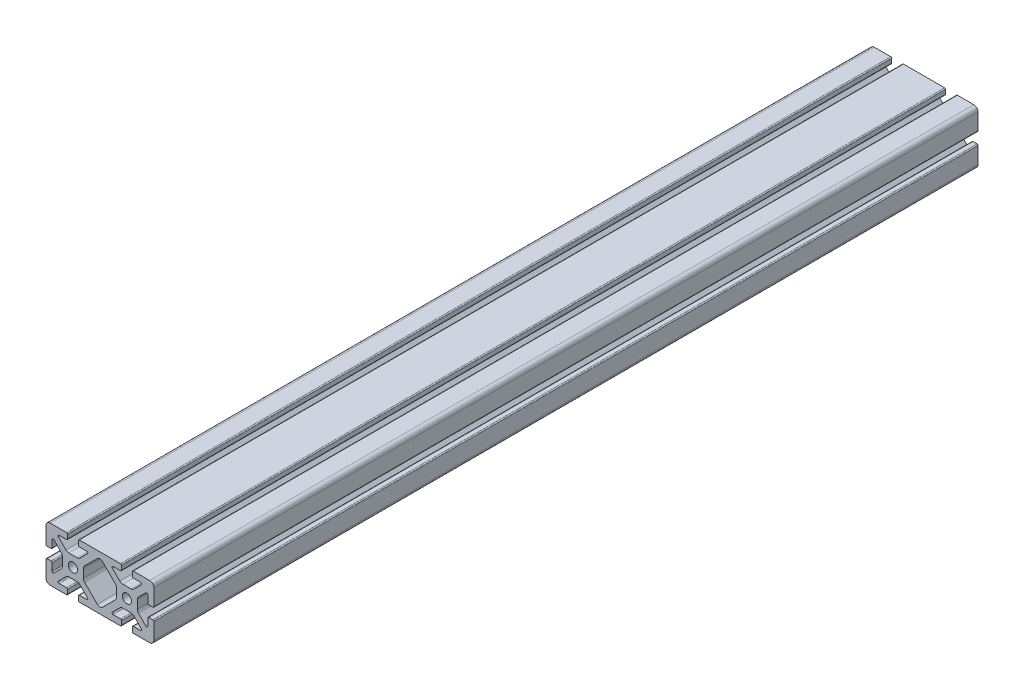
SolidWorks part; units mm, degrees
ref_plane "Front Plane" through (0, 0, 0) normal (0, 0, 1) x (1, 0, 0)
ref_plane "Top Plane" through (0, 0, 0) normal (0, 1, 0) x (1, 0, 0)
ref_plane "Right Plane" through (0, 0, 0) normal (1, 0, 0) x (0, 0, -1)
sketch "Sketch1" plane through (0, 0, 0) normal (0, 0, 1) x (1, 0, 0)
  line L2 (-39.878, 16.891) -> (-39.878, 4.7625)
  line L3 (-36.83, 19.939) -> (-24.7015, 19.939)
  line L4 (-23.9395, 19.177) -> (-23.9395, 16.2052)
  line L5 (-24.7015, 15.4432) -> (-30.1625, 15.4432)
  line L6 (-30.7013, 14.1424) -> (-25.133, 8.5741)
  line L7 (-34.0814, 10.7623) -> (-28.5131, 5.194)
  line L8 (-35.3822, 10.2235) -> (-35.3822, 4.7625)
  line L9 (-36.1442, 4.0005) -> (-39.116, 4.0005)
  line L11 (-23.0136, 7.6962) -> (-16.8644, 7.6962)
  line L12 (-27.6352, 3.0746) -> (-27.6352, -3.0746)
  line L13 (15.1765, 19.939) -> (-15.1765, 19.939)
  line L14 (-15.9385, 19.177) -> (-15.9385, 16.2052)
  line L15 (-15.1765, 15.4432) -> (-9.7155, 15.4432)
  line L16 (-12.2428, 3.0746) -> (-12.2428, -3.0746)
  line L17 (-9.1767, 14.1424) -> (-14.745, 8.5741)
  line L18 (-1.9047, 14.6543) -> (-11.3649, 5.194)
  line L19 (-36.1442, -4.0005) -> (-39.116, -4.0005)
  line L20 (-35.3822, -10.2235) -> (-35.3822, -4.7625)
  line L21 (-34.0814, -10.7623) -> (-28.5131, -5.194)
  line L22 (-30.7013, -14.1424) -> (-25.133, -8.5741)
  line L23 (-24.7015, -15.4432) -> (-30.1625, -15.4432)
  line L24 (-23.9395, -19.177) -> (-23.9395, -16.2052)
  line L25 (-36.83, -19.939) -> (-24.7015, -19.939)
  line L26 (-39.878, -16.891) -> (-39.878, -4.7625)
  line L27 (15.1765, -19.939) -> (-15.1765, -19.939)
  line L28 (-15.9385, -19.177) -> (-15.9385, -16.2052)
  line L29 (-15.1765, -15.4432) -> (-9.7155, -15.4432)
  line L30 (-9.1767, -14.1424) -> (-14.745, -8.5741)
  line L31 (-1.9047, -14.6543) -> (-11.3649, -5.194)
  line L32 (-23.0136, -7.6962) -> (-16.8644, -7.6962)
  line L34 (23.0136, -7.6962) -> (16.8644, -7.6962)
  line L35 (1.9047, -14.6543) -> (11.3649, -5.194)
  line L36 (9.1767, -14.1424) -> (14.745, -8.5741)
  line L37 (15.1765, -15.4432) -> (9.7155, -15.4432)
  line L38 (15.9385, -19.177) -> (15.9385, -16.2052)
  line L40 (39.878, -16.891) -> (39.878, -4.7625)
  line L41 (36.83, -19.939) -> (24.7015, -19.939)
  line L42 (23.9395, -19.177) -> (23.9395, -16.2052)
  line L43 (24.7015, -15.4432) -> (30.1625, -15.4432)
  line L44 (30.7013, -14.1424) -> (25.133, -8.5741)
  line L45 (34.0814, -10.7623) -> (28.5131, -5.194)
  line L46 (35.3822, -10.2235) -> (35.3822, -4.7625)
  line L47 (36.1442, -4.0005) -> (39.116, -4.0005)
  line L48 (1.9047, 14.6543) -> (11.3649, 5.194)
  line L49 (9.1767, 14.1424) -> (14.745, 8.5741)
  line L50 (12.2428, 3.0746) -> (12.2428, -3.0746)
  line L51 (15.1765, 15.4432) -> (9.7155, 15.4432)
  line L52 (15.9385, 19.177) -> (15.9385, 16.2052)
  line L53 (27.6352, 3.0746) -> (27.6352, -3.0746)
  line L54 (23.0136, 7.6962) -> (16.8644, 7.6962)
  line L55 (36.1442, 4.0005) -> (39.116, 4.0005)
  line L56 (35.3822, 10.2235) -> (35.3822, 4.7625)
  line L57 (34.0814, 10.7623) -> (28.5131, 5.194)
  line L58 (30.7013, 14.1424) -> (25.133, 8.5741)
  line L59 (24.7015, 15.4432) -> (30.1625, 15.4432)
  line L60 (23.9395, 19.177) -> (23.9395, 16.2052)
  line L61 (36.83, 19.939) -> (24.7015, 19.939)
  line L62 (39.878, 16.891) -> (39.878, 4.7625)
  circle A0 centre (-19.939, 0) radius 3.4036
  arc A1 (-39.878, 16.891) -> (-36.83, 19.939) centre (-36.83, 16.891) cw
  arc A2 (-34.0814, 10.7623) -> (-35.3822, 10.2235) centre (-34.6202, 10.2235) ccw
  arc A3 (-30.1625, 15.4432) -> (-30.7013, 14.1424) centre (-30.1625, 14.6812) ccw
  arc A4 (-24.7015, 19.939) -> (-23.9395, 19.177) centre (-24.7015, 19.177) cw
  arc A5 (-39.878, 4.7625) -> (-39.116, 4.0005) centre (-39.116, 4.7625) ccw
  arc A6 (-35.3822, 4.7625) -> (-36.1442, 4.0005) centre (-36.1442, 4.7625) cw
  arc A7 (-23.9395, 16.2052) -> (-24.7015, 15.4432) centre (-24.7015, 16.2052) cw
  arc A8 (-23.0136, 7.6962) -> (-25.133, 8.5741) centre (-23.0136, 10.6934) cw
  arc A9 (-27.6352, 3.0746) -> (-28.5131, 5.194) centre (-30.6324, 3.0746) ccw
  arc A10 (1.9047, 14.6543) -> (-1.9047, 14.6543) centre (0, 12.7496) ccw
  arc A11 (-1.9047, -14.6543) -> (1.9047, -14.6543) centre (0, -12.7496) ccw
  arc A12 (-15.1765, 19.939) -> (-15.9385, 19.177) centre (-15.1765, 19.177) ccw
  arc A13 (-15.9385, 16.2052) -> (-15.1765, 15.4432) centre (-15.1765, 16.2052) ccw
  arc A14 (-16.8644, 7.6962) -> (-14.745, 8.5741) centre (-16.8644, 10.6934) ccw
  arc A15 (-12.2428, 3.0746) -> (-11.3649, 5.194) centre (-9.2456, 3.0746) cw
  arc A16 (-9.7155, 15.4432) -> (-9.1767, 14.1424) centre (-9.7155, 14.6812) cw
  arc A17 (-27.6352, -3.0746) -> (-28.5131, -5.194) centre (-30.6324, -3.0746) cw
  arc A18 (-23.0136, -7.6962) -> (-25.133, -8.5741) centre (-23.0136, -10.6934) ccw
  arc A19 (-23.9395, -16.2052) -> (-24.7015, -15.4432) centre (-24.7015, -16.2052) ccw
  arc A20 (-35.3822, -4.7625) -> (-36.1442, -4.0005) centre (-36.1442, -4.7625) ccw
  arc A21 (-39.878, -4.7625) -> (-39.116, -4.0005) centre (-39.116, -4.7625) cw
  arc A22 (-24.7015, -19.939) -> (-23.9395, -19.177) centre (-24.7015, -19.177) ccw
  arc A23 (-30.1625, -15.4432) -> (-30.7013, -14.1424) centre (-30.1625, -14.6812) cw
  arc A24 (-34.0814, -10.7623) -> (-35.3822, -10.2235) centre (-34.6202, -10.2235) cw
  arc A25 (-39.878, -16.891) -> (-36.83, -19.939) centre (-36.83, -16.891) ccw
  arc A26 (-9.7155, -15.4432) -> (-9.1767, -14.1424) centre (-9.7155, -14.6812) ccw
  arc A27 (-15.1765, -19.939) -> (-15.9385, -19.177) centre (-15.1765, -19.177) cw
  arc A28 (-15.9385, -16.2052) -> (-15.1765, -15.4432) centre (-15.1765, -16.2052) cw
  arc A29 (-16.8644, -7.6962) -> (-14.745, -8.5741) centre (-16.8644, -10.6934) cw
  arc A30 (-12.2428, -3.0746) -> (-11.3649, -5.194) centre (-9.2456, -3.0746) ccw
  arc A31 (12.2428, -3.0746) -> (11.3649, -5.194) centre (9.2456, -3.0746) cw
  arc A32 (16.8644, -7.6962) -> (14.745, -8.5741) centre (16.8644, -10.6934) ccw
  arc A33 (15.9385, -16.2052) -> (15.1765, -15.4432) centre (15.1765, -16.2052) ccw
  arc A34 (15.1765, -19.939) -> (15.9385, -19.177) centre (15.1765, -19.177) ccw
  arc A35 (9.7155, -15.4432) -> (9.1767, -14.1424) centre (9.7155, -14.6812) cw
  arc A36 (39.878, -16.891) -> (36.83, -19.939) centre (36.83, -16.891) cw
  arc A37 (34.0814, -10.7623) -> (35.3822, -10.2235) centre (34.6202, -10.2235) ccw
  arc A38 (30.1625, -15.4432) -> (30.7013, -14.1424) centre (30.1625, -14.6812) ccw
  arc A39 (24.7015, -19.939) -> (23.9395, -19.177) centre (24.7015, -19.177) cw
  arc A40 (39.878, -4.7625) -> (39.116, -4.0005) centre (39.116, -4.7625) ccw
  arc A41 (35.3822, -4.7625) -> (36.1442, -4.0005) centre (36.1442, -4.7625) cw
  arc A42 (23.9395, -16.2052) -> (24.7015, -15.4432) centre (24.7015, -16.2052) cw
  arc A43 (23.0136, -7.6962) -> (25.133, -8.5741) centre (23.0136, -10.6934) cw
  arc A44 (27.6352, -3.0746) -> (28.5131, -5.194) centre (30.6324, -3.0746) ccw
  arc A45 (9.7155, 15.4432) -> (9.1767, 14.1424) centre (9.7155, 14.6812) ccw
  arc A46 (12.2428, 3.0746) -> (11.3649, 5.194) centre (9.2456, 3.0746) ccw
  arc A47 (16.8644, 7.6962) -> (14.745, 8.5741) centre (16.8644, 10.6934) cw
  arc A48 (15.9385, 16.2052) -> (15.1765, 15.4432) centre (15.1765, 16.2052) cw
  arc A49 (15.1765, 19.939) -> (15.9385, 19.177) centre (15.1765, 19.177) cw
  arc A50 (27.6352, 3.0746) -> (28.5131, 5.194) centre (30.6324, 3.0746) cw
  arc A51 (23.0136, 7.6962) -> (25.133, 8.5741) centre (23.0136, 10.6934) ccw
  arc A52 (23.9395, 16.2052) -> (24.7015, 15.4432) centre (24.7015, 16.2052) ccw
  arc A53 (35.3822, 4.7625) -> (36.1442, 4.0005) centre (36.1442, 4.7625) ccw
  arc A54 (39.878, 4.7625) -> (39.116, 4.0005) centre (39.116, 4.7625) cw
  arc A55 (24.7015, 19.939) -> (23.9395, 19.177) centre (24.7015, 19.177) ccw
  arc A56 (30.1625, 15.4432) -> (30.7013, 14.1424) centre (30.1625, 14.6812) cw
  arc A57 (34.0814, 10.7623) -> (35.3822, 10.2235) centre (34.6202, 10.2235) cw
  arc A58 (39.878, 16.891) -> (36.83, 19.939) centre (36.83, 16.891) ccw
  circle A59 centre (19.939, 0) radius 3.4036
  point P185 (19.939, 7.6962)
extrude "Boss-Extrude1" add sketch "Sketch1" along normal mid plane 609.6
